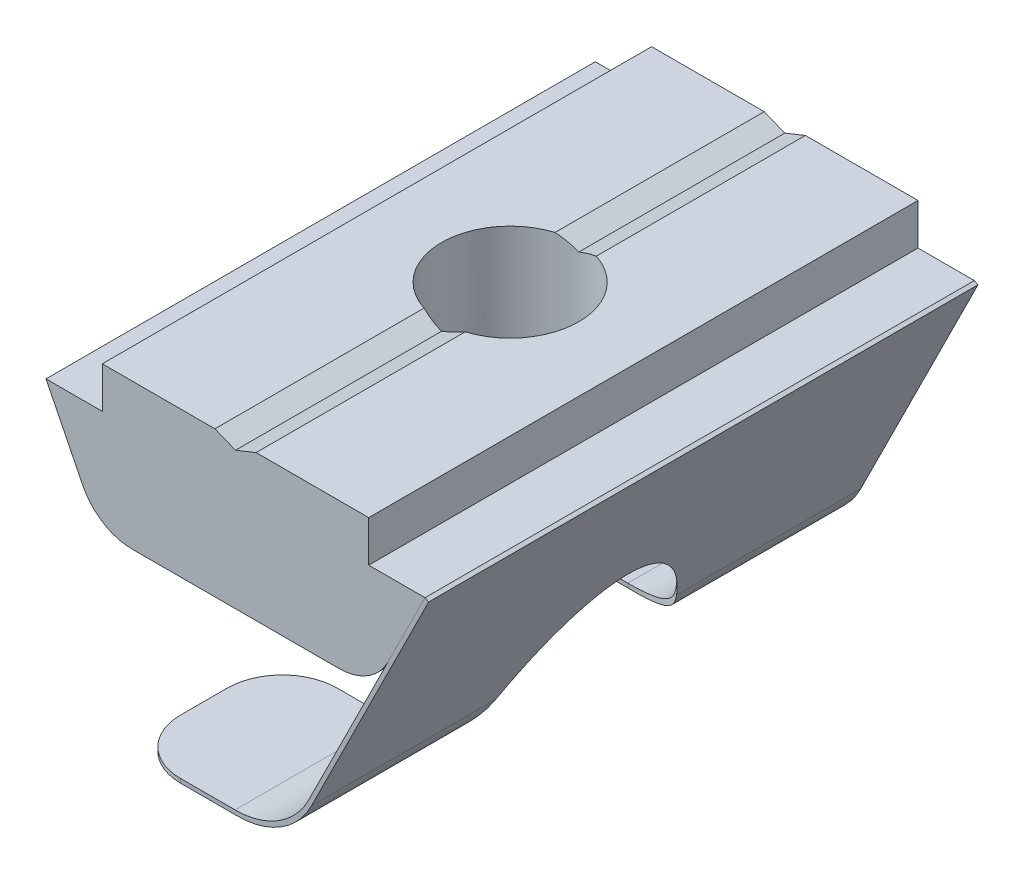
SolidWorks part; units mm, degrees
ref_plane "Спереди" through (0, 0, 0) normal (0, 0, 1) x (1, 0, 0)
ref_plane "Сверху" through (0, 0, 0) normal (0, 1, 0) x (1, 0, 0)
ref_plane "Справа" through (0, 0, 0) normal (1, 0, 0) x (0, 0, -1)
sketch "Эскиз1" plane through (0, 0, 0) normal (0, 0, 1) x (1, 0, 0)
  line L0 (0, 0) -> (0.75, 0.3)
  line L5 (3.7678, -5) -> (-3.7678, -5)
  line L6 (0, 0) -> (0, -5) construction
  line L17 (6.9, -1.2) -> (5.5576, -3.8924)
  line L18 (0.75, 0.3) -> (4.85, 0.3)
  line L19 (4.85, 0.3) -> (4.85, -1.2)
  line L20 (4.85, -1.2) -> (6.9, -1.2)
  line L21 (-4.85, -1.2) -> (-6.9, -1.2)
  line L22 (-4.85, 0.3) -> (-4.85, -1.2)
  line L23 (-0.75, 0.3) -> (-4.85, 0.3)
  line L24 (-6.9, -1.2) -> (-5.5576, -3.8924)
  line L25 (0, 0) -> (-0.75, 0.3)
  arc A0 (5.5576, -3.8924) -> (3.7678, -5) centre (3.7678, -3) cw
  arc A1 (-5.5576, -3.8924) -> (-3.7678, -5) centre (-3.7678, -3) ccw
  dimension "D9" = 2
  dimension "D1" = 6.9
  dimension "D2" = 4.85
  dimension "D3" = 1.5
  dimension "D4" = 5.3
  dimension "D5" = 0.3
  dimension "D6" = 26.5
  dimension "D8" = 0.75
extrude "Бобышка-Вытянуть1" add sketch "Эскиз1" along normal mid plane 20
sketch "Эскиз2" plane through (0, 0, 0) normal (0, 0, 1) x (1, 0, 0)
  line L0 (6.9, -1.2) -> (2.6677, -9.6886)
  line L2 (0.0758, -11.5) -> (-4, -11.5)
  line L3 (4.85, 0.3) -> (0.75, 0.3) construction
  line L4 (7.0342, -1.2669) -> (2.7606, -9.8386)
  line L5 (-0.0171, -11.35) -> (-4, -11.35)
  line L6 (3.4149, -11.35) -> (-4, -11.35) construction
  line L7 (3.4149, -11.5) -> (-4, -11.5) construction
  line L8 (7.0342, -1.2669) -> (-0.577, -16.5326) construction
  line L9 (6.9, -1.2) -> (-0.7112, -16.4657) construction
  line L10 (-4, -11.35) -> (-4, -11.5)
  line L11 (6.9, -1.2) -> (7.0342, -1.2669)
  arc A0 (0.0758, -11.5) -> (2.7606, -9.8386) centre (0.0758, -8.5) ccw
  arc A1 (2.6677, -9.6886) -> (-0.0171, -11.35) centre (-0.0171, -8.35) cw
  dimension "D5" = 3
  dimension "D1" = 10.9
  dimension "D2" = 11.8
  dimension "D3" = 0.15
  dimension "D4" = 0.15
extrude "Бобышка-Вытянуть2" add sketch "Эскиз2" along normal mid plane 20 separate body
sketch "Эскиз3" plane through (0, -5, 0) normal (0, -1, 0) x (1, 0, 0)
  line L0 (0, 4.3) -> (-5.5576, 4.3)
  line L1 (-5.5576, 10) -> (-5.5576, -10) construction
  line L2 (-5.5576, 4.3) -> (-5.5576, -4.3)
  line L3 (-5.5576, -4.3) -> (0, -4.3)
  arc A0 (0, -4.3) -> (0, 4.3) centre (0, 0) ccw
  dimension "D1" = 8.6
extrude "Вырез-Вытянуть1" cut sketch "Эскиз3" along normal blind 20
fillet "Скругление1" radius 2 4 edges at (-4, -11.425, 10) (-4, -11.425, 4.3) (-4, -11.425, -4.3) (-4, -11.425, -10)
hole_wizard "Отверстие обработанное метчиком M61" positions "Трехмерный эскиз1" profile "Эскиз4" tap size "M6" standard "DIN" end condition through all
sketch3d "Трехмерный эскиз1"
  point P0 (0, 0.3, 0)
  dimension "D1" = 10
  dimension "D2" = 4.85
sketch "Эскиз4" plane through (0, 0.3, 0) normal (1, 0, 0) x (0, 0, 1)
  line L0 (0, 0) -> (0, 11.8)
  line L1 (0, 11.8) -> (2.5, 11.8)
  line L2 (2.5, 11.8) -> (2.5, 0)
  line L5 (2.5, 0) -> (0, 0)
  line L11 (0, -6.35) -> (0, 107.95) construction
  dimension "Диаметр проходного сверла" = 5
  dimension "Глубина проходного сверла" = 11.8
cosmetic thread "Отверстие резьбы1"
